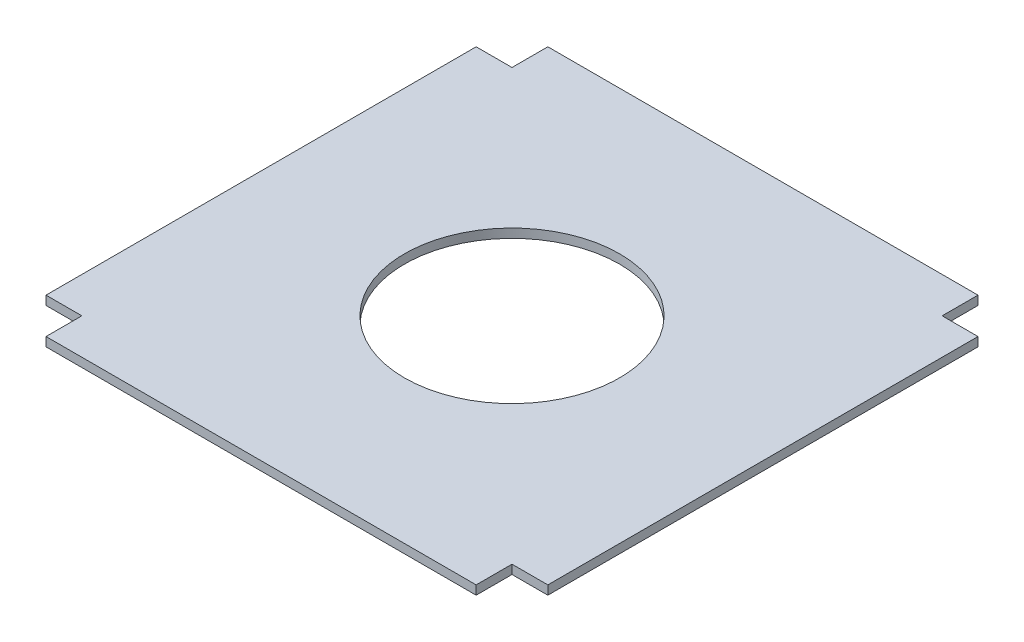
SolidWorks part; units mm, degrees
ref_plane "Front Plane" through (0, 0, 0) normal (0, 0, 1) x (1, 0, 0)
ref_plane "Top Plane" through (0, 0, 0) normal (0, 1, 0) x (1, 0, 0)
ref_plane "Right Plane" through (0, 0, 0) normal (1, 0, 0) x (0, 0, -1)
sketch "Sketch1" plane through (0, 0, 0) normal (0, 1, 0) x (1, 0, 0)
  line L0 (0, 0) -> (0, -25.4)
  line L1 (0, -25.4) -> (-304.8, -25.4)
  line L2 (-304.8, -25.4) -> (-304.8, 0)
  line L3 (-304.8, 0) -> (-330.2, 0)
  line L4 (-330.2, 0) -> (-330.2, 304.8)
  line L5 (-330.2, 304.8) -> (-304.8, 304.8)
  line L6 (-304.8, 304.8) -> (-304.8, 330.2)
  line L7 (-304.8, 330.2) -> (0, 330.2)
  line L8 (0, 330.2) -> (0, 304.8)
  line L9 (0, 304.8) -> (25.4, 304.8)
  line L10 (25.4, 304.8) -> (25.4, 0)
  line L11 (25.4, 0) -> (0, 0)
  line L12 (-304.8, 0) -> (0, 0) construction
  line L13 (0, 304.8) -> (-304.8, 304.8) construction
  line L14 (-304.8, 304.8) -> (-304.8, 0) construction
  line L15 (0, 0) -> (0, 304.8) construction
  line L16 (-152.4, 152.4) -> (-152.4, 0) construction
  line L17 (-152.4, 152.4) -> (-304.8, 152.4) construction
  circle A0 centre (-152.4, 152.4) radius 76.2
  dimension "D7" = 152.4
  dimension "D1" = 304.8
  dimension "D2" = 304.8
  dimension "D3" = 25.4
  dimension "D4" = 25.4
  dimension "D5" = 25.4
  dimension "D6" = 25.4
extrude "Boss-Extrude1" add sketch "Sketch1" along normal blind 6.35
equation "\"D2@Sketch1\"=\"D1@Sketch1\""
equation "\"D4@Sketch1\"=\"D3@Sketch1\""
equation "\"D5@Sketch1\"=\"D3@Sketch1\""
equation "\"D6@Sketch1\"=\"D3@Sketch1\""
